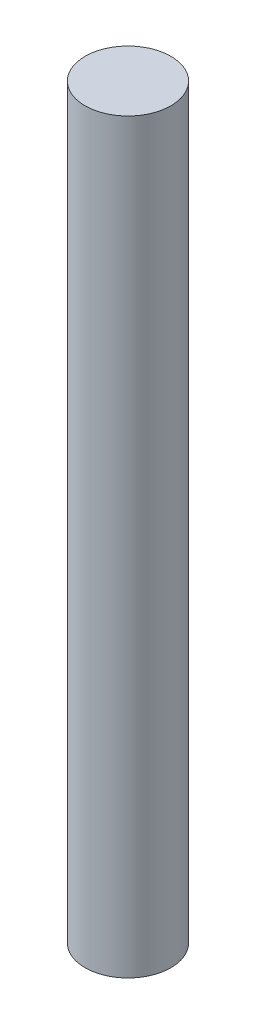
SolidWorks part; units mm, degrees
ref_plane "Front Plane" through (0, 0, 0) normal (0, 0, 1) x (1, 0, 0)
ref_plane "Top Plane" through (0, 0, 0) normal (0, 1, 0) x (1, 0, 0)
ref_plane "Right Plane" through (0, 0, 0) normal (1, 0, 0) x (0, 0, -1)
sketch "Sketch1" plane through (0, 0, 0) normal (0, 1, 0) x (1, 0, 0)
  circle A0 centre (0, 0) radius 2.5
  dimension "D1" = 5
extrude "Boss-Extrude1" add sketch "Sketch1" along normal blind 43.5
